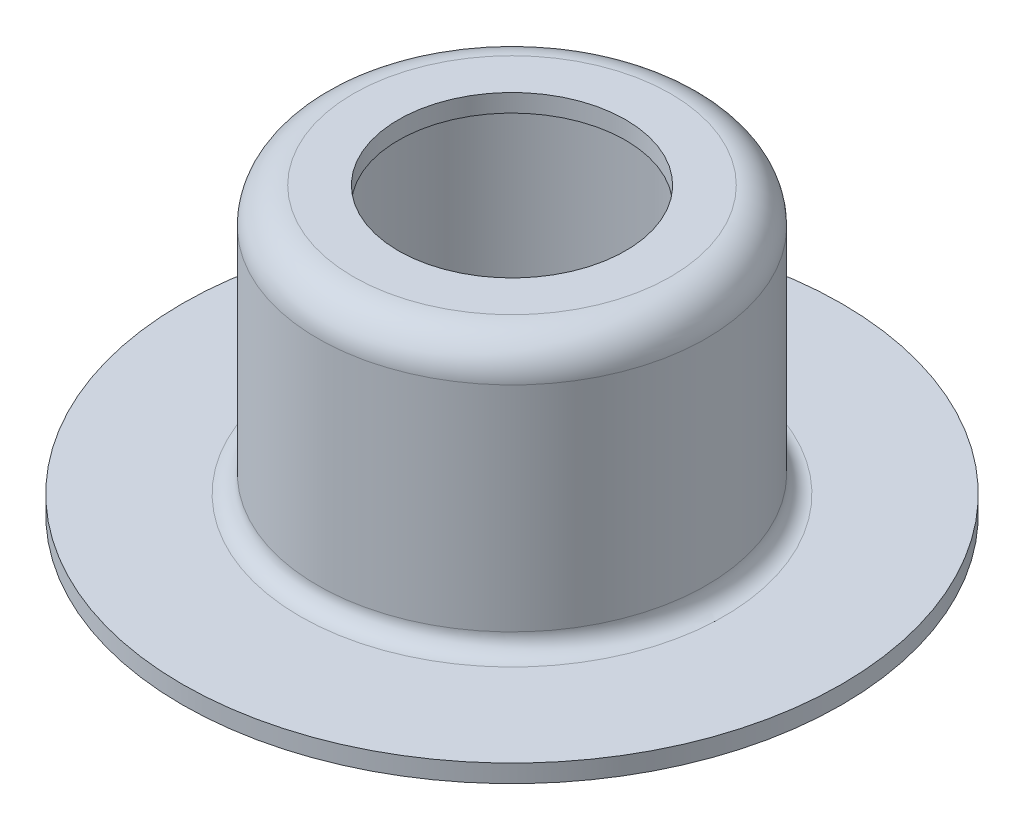
SolidWorks part; units mm, degrees
material "AISI 316 Stainless Steel Sheet (SS)"
ref_plane "Front Plane" through (0, 0, 0) normal (0, 0, 1) x (1, 0, 0)
ref_plane "Top Plane" through (0, 0, 0) normal (0, 1, 0) x (1, 0, 0)
ref_plane "Right Plane" through (0, 0, 0) normal (1, 0, 0) x (0, 0, -1)
sketch "Sketch1" plane through (0, 0, 0) normal (0, 0, 1) x (1, 0, 0)
  line L0 (0, 0) -> (0, 70.8619) construction
  line L1 (-18.5, 0) -> (-10.9, 0)
  line L2 (-8.9, 2) -> (-8.9, 14)
  line L3 (-7.9, 15) -> (-6.375, 15)
  line L4 (-6.375, 15) -> (-6.375, 16)
  line L5 (-6.375, 16) -> (-8.9, 16)
  line L6 (-10.9, 14) -> (-10.9, 2)
  line L7 (-11.9, 1) -> (-18.5, 1)
  line L8 (-18.5, 1) -> (-18.5, 0)
  arc A0 (-10.9, 2) -> (-11.9, 1) centre (-11.9, 2) cw
  arc A1 (-8.9, 14) -> (-7.9, 15) centre (-7.9, 14) cw
  arc A2 (-10.9, 0) -> (-8.9, 2) centre (-10.9, 2) ccw
  arc A3 (-8.9, 16) -> (-10.9, 14) centre (-8.9, 14) ccw
  point P5 (-16.3915, 4)
  point P12 (-23.4525, 0)
  point P13 (-4.0507, 4)
  point P18 (-8.9, 15)
  point P21 (-8.9, 0)
  dimension "D8" = 1
  dimension "D9" = 2
  dimension "D1" = 8.9
  dimension "D2" = 1
  dimension "D3" = 15
  dimension "D4" = 6.375
  dimension "D5" = 2
  dimension "D6" = 1
  dimension "D7" = 18.5
revolve "Revolve1" add sketch "Sketch1" angle 360 about L0
equation "\"D1@Sketch1\"=(17.75+0.05)/2"
equation "\"D4@Sketch1\"=(16.75-4)/2"
equation "\"D7@Sketch1\"=37/2"
